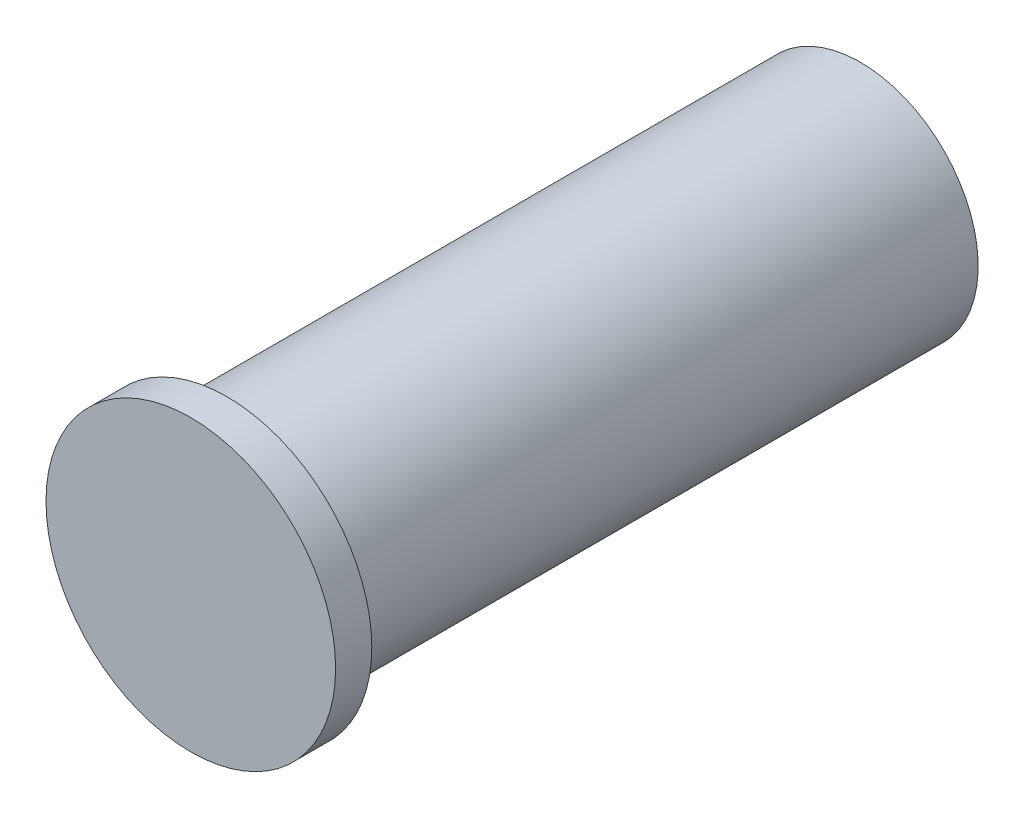
SolidWorks part; units mm, degrees
ref_plane "Front Plane" through (0, 0, 0) normal (0, 0, 1) x (1, 0, 0)
ref_plane "Top Plane" through (0, 0, 0) normal (0, 1, 0) x (1, 0, 0)
ref_plane "Right Plane" through (0, 0, 0) normal (1, 0, 0) x (0, 0, -1)
sketch "Sketch1" plane through (0, 0, 0) normal (0, 0, 1) x (1, 0, 0)
  circle A0 centre (0, 0) radius 1.6
  dimension "D1" = 3.2
extrude "Boss-Extrude1" add sketch "Sketch1" along normal blind 0.4
sketch "Sketch2" plane through (0, 0, 0) normal (0, 0, -1) x (-1, 0, 0)
  circle A0 centre (0, 0) radius 1.3
  dimension "D1" = 2.6
extrude "Boss-Extrude2" add sketch "Sketch2" along normal blind 7
